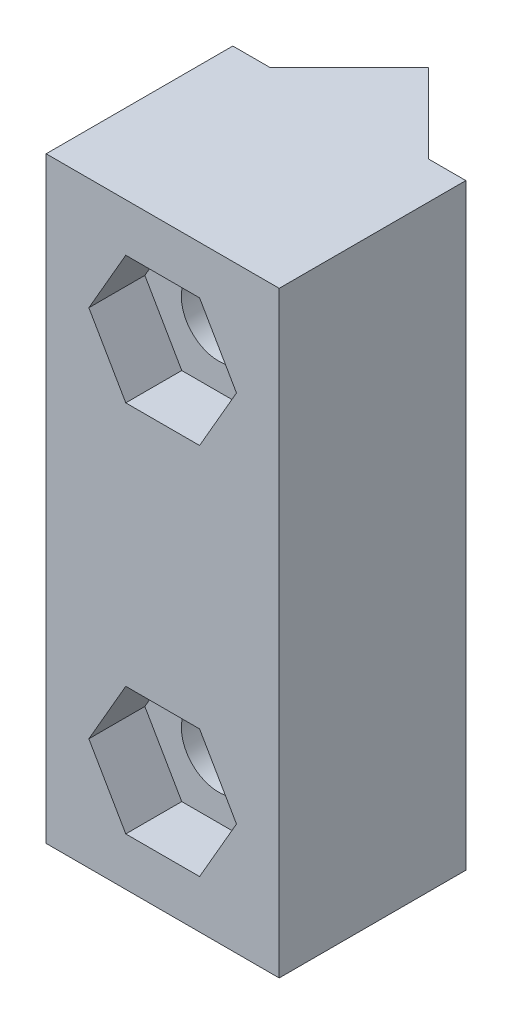
SolidWorks part; units mm, degrees
ref_plane "Front Plane" through (0, 0, 0) normal (0, 0, 1) x (1, 0, 0)
ref_plane "Top Plane" through (0, 0, 0) normal (0, 1, 0) x (1, 0, 0)
ref_plane "Right Plane" through (0, 0, 0) normal (1, 0, 0) x (0, 0, -1)
sketch "Sketch2" plane through (0, 0, 0) normal (0, 1, 0) x (1, 0, 0)
  line L0 (-4.9891, 0) -> (-2.9891, 0)
  line L1 (-2.9891, 0) -> (1.2536, 4.2426)
  line L2 (1.2536, 4.2426) -> (5.4962, 0)
  line L3 (5.4962, 0) -> (7.4962, 0)
  line L4 (7.4962, 0) -> (7.4962, -10)
  line L5 (7.4962, -10) -> (-4.9891, -10)
  line L6 (-4.9891, -10) -> (-4.9891, 0)
  line L8 (-12.6225, 9.1032) -> (12.3775, 9.1032) construction
  line L9 (-12.6225, 9.1032) -> (-12.6225, 3.0072) construction
  line L10 (-12.6225, 3.0072) -> (12.3775, 3.0072) construction
  line L11 (12.3775, 9.1032) -> (12.3775, 3.0072) construction
  point P12 (-1.2826, 4.2426)
  point P13 (-5.5451, 0)
  point P14 (0, 0)
  point P15 (4.2496, 4.2426)
  point P16 (0, 0)
  dimension "D1" = 6.096
  dimension "D2" = 25
  dimension "D3" = 6
  dimension "D4" = 2
  dimension "D5" = 10
extrude "Boss-Extrude1" add sketch "Sketch2" along normal blind 25 and the other way blind 7 contours L6 L0 L1 L2 L3 L4 L5
sketch "Sketch3" plane through (0, 0, 10) normal (0, 0, 1) x (1, 0, 0)
  line L0 (1.2536, -7) -> (1.2536, 25) construction
  line L1 (7.4962, 25) -> (-4.9891, 25) construction
  line L2 (7.4962, -7) -> (-4.9891, -7) construction
  circle A0 centre (1.2536, 19) radius 2
  circle A1 centre (1.2536, -1) radius 2
  dimension "D3" = 4
  dimension "D1" = 6
  dimension "D2" = 6
extrude "Cut-Extrude1" cut sketch "Sketch3" against normal blind 25
sketch "Sketch4" plane through (0, 0, 10) normal (0, 0, 1) x (1, 0, 0)
  line L0 (7.4962, 9) -> (-4.9891, 9) construction
  line L1 (5.2084, -1) -> (3.231, 2.425)
  line L2 (3.231, 2.425) -> (-0.7239, 2.425)
  line L3 (-0.7239, 2.425) -> (-2.7013, -1)
  line L4 (-2.7013, -1) -> (-0.7239, -4.425)
  line L5 (-0.7239, -4.425) -> (3.231, -4.425)
  line L6 (3.231, -4.425) -> (5.2084, -1)
  line L7 (7.4962, -7) -> (7.4962, 25) construction
  line L8 (-4.9891, -7) -> (-4.9891, 25) construction
  line L9 (3.231, 22.425) -> (5.2084, 19)
  line L10 (-0.7239, 22.425) -> (3.231, 22.425)
  line L11 (-2.7013, 19) -> (-0.7239, 22.425)
  line L12 (-0.7239, 15.575) -> (-2.7013, 19)
  line L13 (3.231, 15.575) -> (-0.7239, 15.575)
  line L14 (5.2084, 19) -> (3.231, 15.575)
  circle A0 centre (1.2536, -1) radius 3.425 construction
  dimension "D1" = 6.85
extrude "Cut-Extrude2" cut sketch "Sketch4" against normal blind 3
sketch "Sketch5" plane through (0, 0, 10) normal (0, 0, 1) x (1, 0, 0)
  circle A0 centre (1.2536, -1) radius 3.505
  dimension "D1" = 7.01
equation "\"D2@Sketch3\"=\"D1@Sketch3\""
